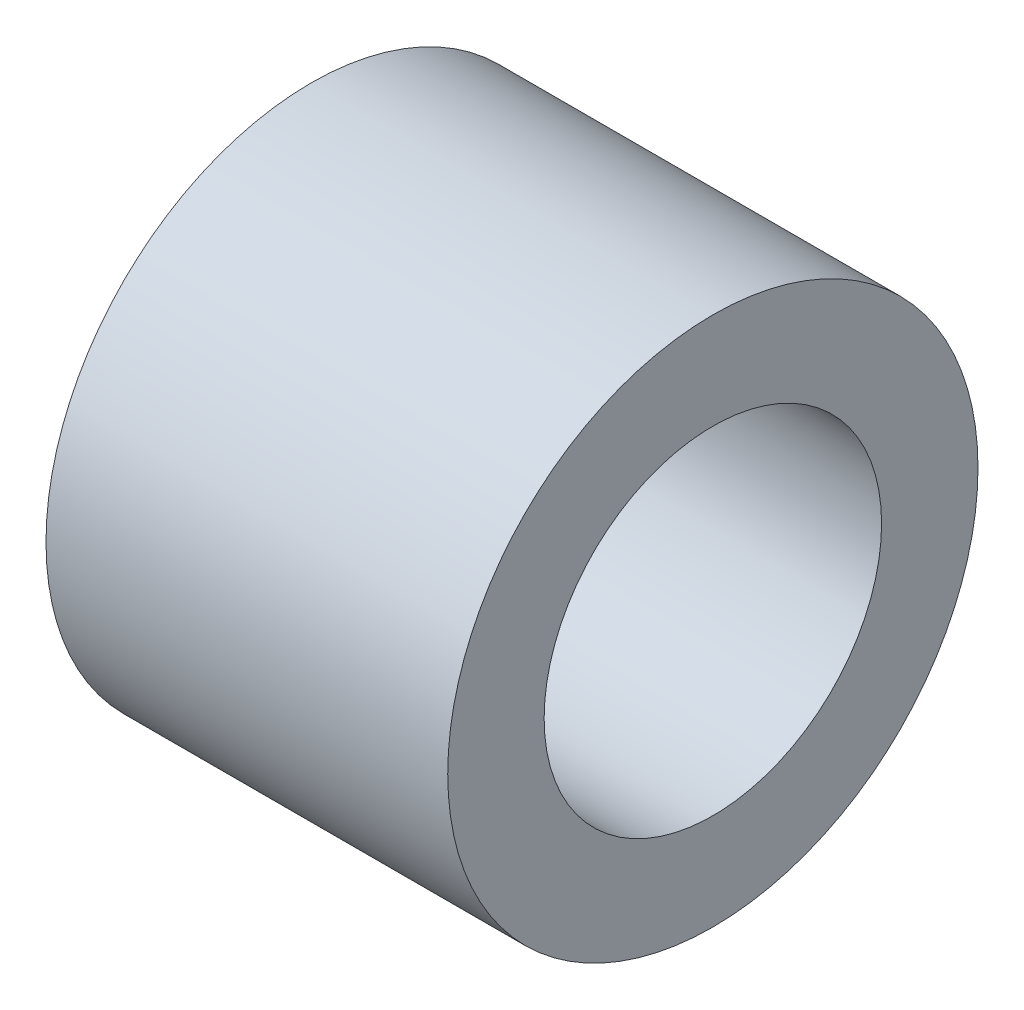
SolidWorks part; units mm, degrees
ref_plane "Front Plane" through (0, 0, 0) normal (0, 0, 1) x (1, 0, 0)
ref_plane "Top Plane" through (0, 0, 0) normal (0, 1, 0) x (1, 0, 0)
ref_plane "Right Plane" through (0, 0, 0) normal (1, 0, 0) x (0, 0, -1)
sketch "Sketch1" plane through (0, 0, 0) normal (1, 0, 0) x (0, 0, -1)
  circle A0 centre (0, 0) radius 3.3
  circle A1 centre (0, 0) radius 2.1
  dimension "D1" = 4.2
  dimension "D2" = 1.2
extrude "Boss-Extrude1" add sketch "Sketch1" along normal blind 5
